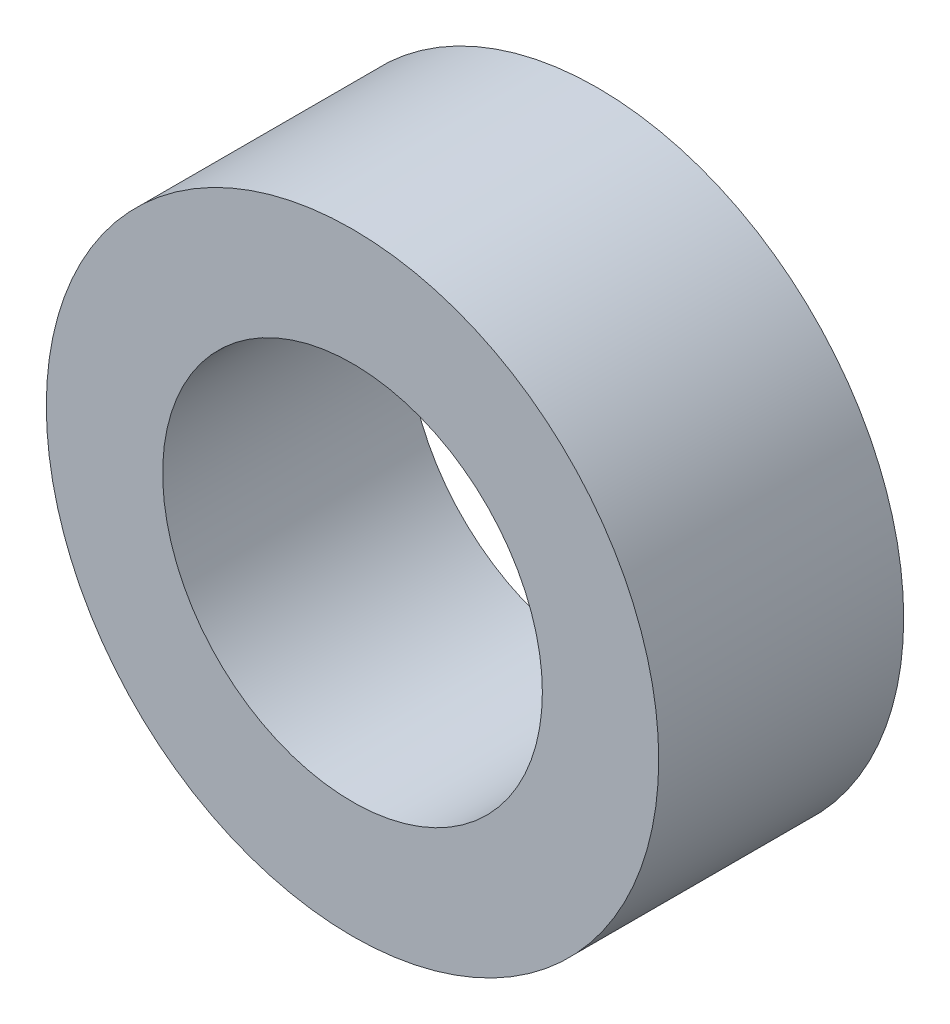
SolidWorks part; units mm, degrees
ref_plane "正面" through (0, 0, 0) normal (0, 0, 1) x (1, 0, 0)
ref_plane "平面" through (0, 0, 0) normal (0, 1, 0) x (1, 0, 0)
ref_plane "右側面" through (0, 0, 0) normal (1, 0, 0) x (0, 0, -1)
sketch "ｽｹｯﾁ1" plane through (0, 0, 0) normal (0, 0, 1) x (1, 0, 0)
  circle A0 centre (0, 0) radius 3.1
  circle A1 centre (0, 0) radius 5
  dimension "D1" = 6.2
  dimension "D2" = 10
extrude "ﾎﾞｽ - 押し出し1" add sketch "ｽｹｯﾁ1" along normal blind 4
